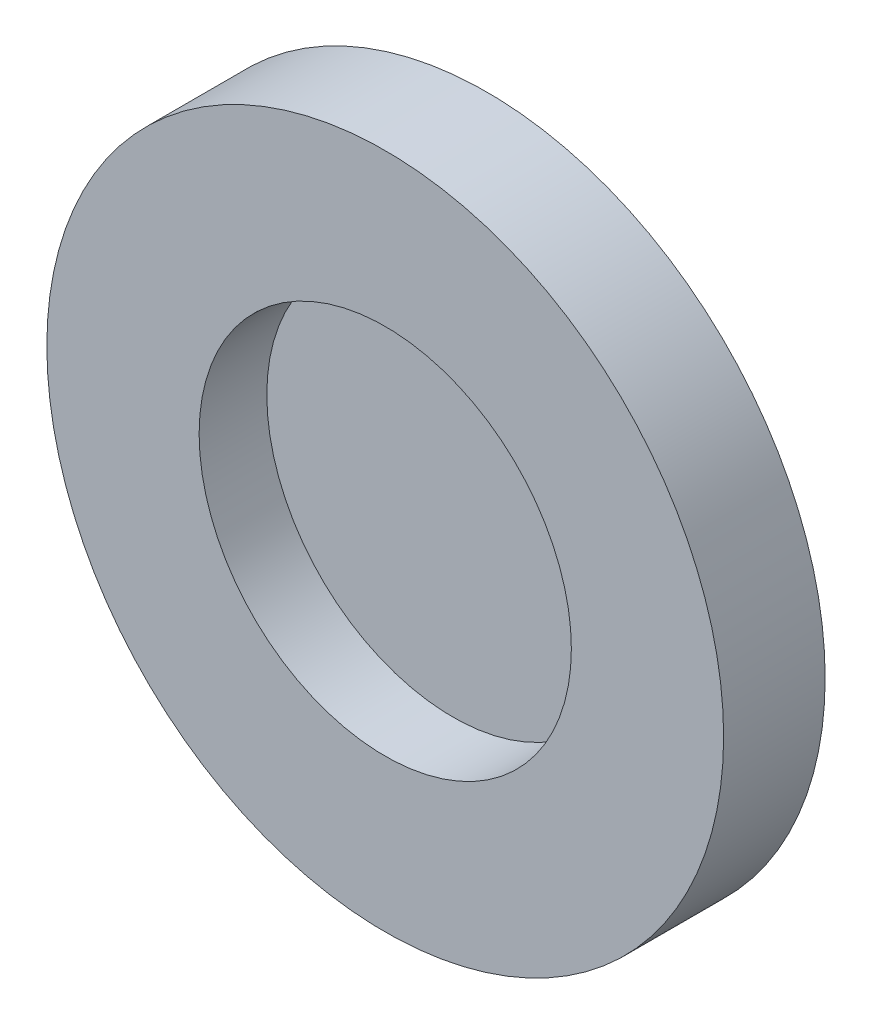
SolidWorks part; units mm, degrees
ref_plane "Front Plane" through (0, 0, 0) normal (0, 0, 1) x (1, 0, 0)
ref_plane "Top Plane" through (0, 0, 0) normal (0, 1, 0) x (1, 0, 0)
ref_plane "Right Plane" through (0, 0, 0) normal (1, 0, 0) x (0, 0, -1)
sketch "Sketch1" plane through (0, 0, 0) normal (0, 0, 1) x (1, 0, 0)
  circle A0 centre (0, 0) radius 5.5
  circle A1 centre (0, 0) radius 10
  dimension "D1" = 11
  dimension "D2" = 20
extrude "Boss-Extrude1" add sketch "Sketch1" along normal blind 2
sketch "Sketch2" plane through (0, 0, 0) normal (0, 0, -1) x (-1, 0, 0)
  circle A0 centre (0, 0) radius 10 construction
  circle A1 centre (0, 0) radius 10
extrude "Boss-Extrude2" add sketch "Sketch2" along normal blind 1
